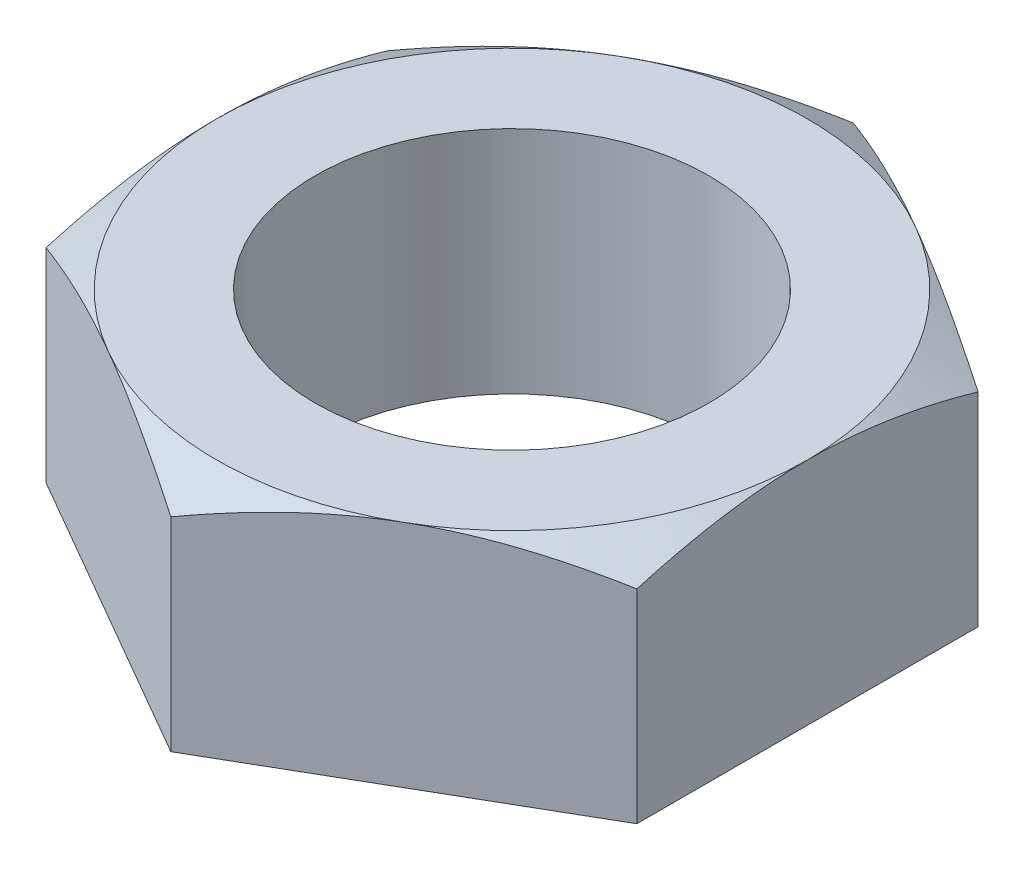
SolidWorks part; units mm, degrees
ref_plane "Front Plane" through (0, 0, 0) normal (0, 0, 1) x (1, 0, 0)
ref_plane "Top Plane" through (0, 0, 0) normal (0, 1, 0) x (1, 0, 0)
ref_plane "Right Plane" through (0, 0, 0) normal (1, 0, 0) x (0, 0, -1)
sketch "Sketch1" plane through (0, 0, 0) normal (0, 1, 0) x (1, 0, 0)
  line L1 (-7.1438, 4.1244) -> (-7.1438, -4.1244)
  line L2 (-7.1438, -4.1244) -> (0, -8.2489)
  line L3 (0, -8.2489) -> (7.1437, -4.1244)
  line L4 (7.1437, -4.1244) -> (7.1437, 4.1244)
  line L5 (7.1437, 4.1244) -> (0, 8.2489)
  line L6 (0, 8.2489) -> (-7.1438, 4.1244)
  circle A0 centre (0, 0) radius 7.1438 construction
  circle A1 centre (0, 0) radius 4.7625
  dimension "Thread Size" = 9.525
  dimension "Hex" = 14.2875
extrude "Boss-Extrude1" add sketch "Sketch1" along normal mid plane 5.5562
sketch "Sketch5" plane through (0, 2.7781, 0) normal (0, 1, 0) x (1, 0, 0)
  circle A0 centre (0, 0) radius 7.1438 construction
  circle A1 centre (0, 0) radius 7.1438
extrude "Cut-Extrude2" cut sketch "Sketch5" against normal through all draft 60 flip side to cut
